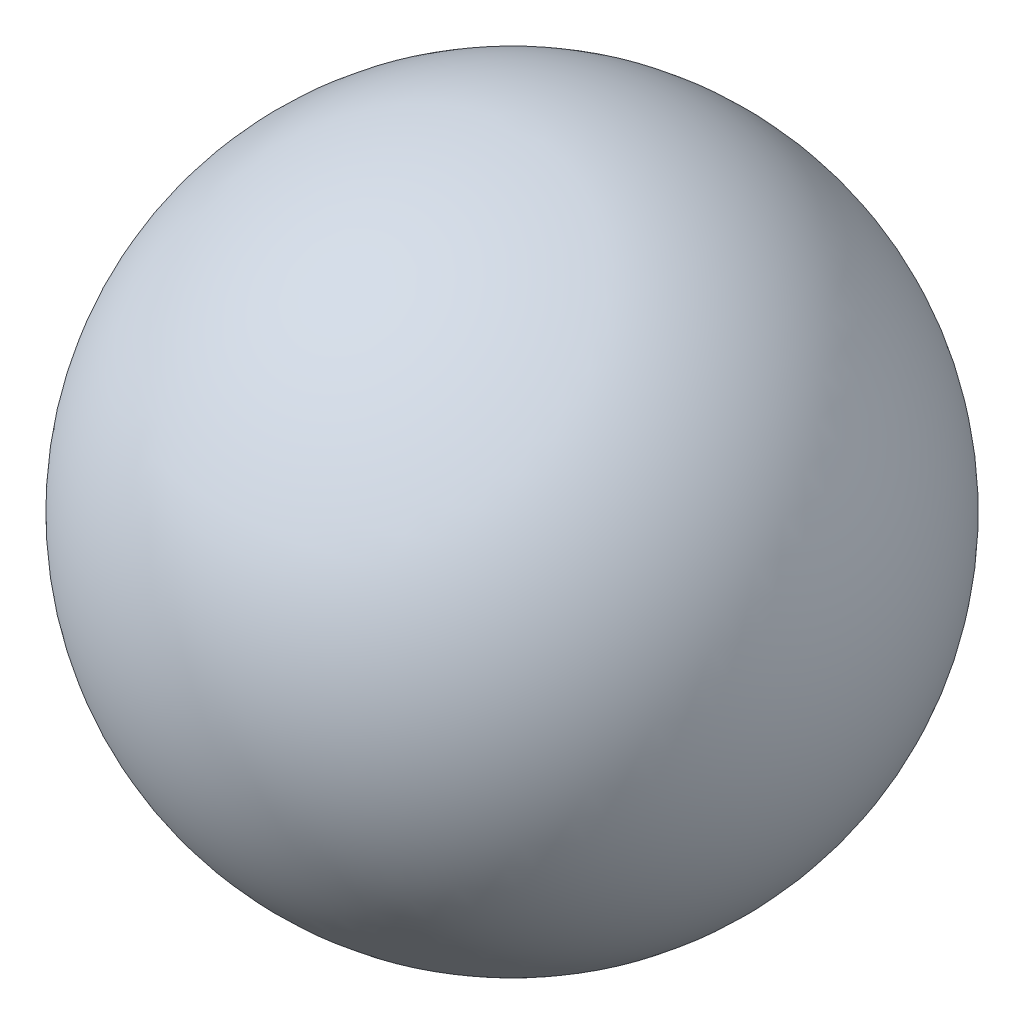
SolidWorks part; units mm, degrees
ref_plane "Front Plane" through (0, 0, 0) normal (0, 0, 1) x (1, 0, 0)
ref_plane "Top Plane" through (0, 0, 0) normal (0, 1, 0) x (1, 0, 0)
ref_plane "Right Plane" through (0, 0, 0) normal (1, 0, 0) x (0, 0, -1)
sketch "Sketch1" plane through (0, 0, 0) normal (0, 0, 1) x (1, 0, 0)
  line L0 (0, 7.5) -> (0, -7.5)
  arc A0 (0, -7.5) -> (0, 7.5) centre (0, 0) ccw
  dimension "D1" = 15
revolve "Revolve3" add sketch "Sketch1" angle 360 about L0
